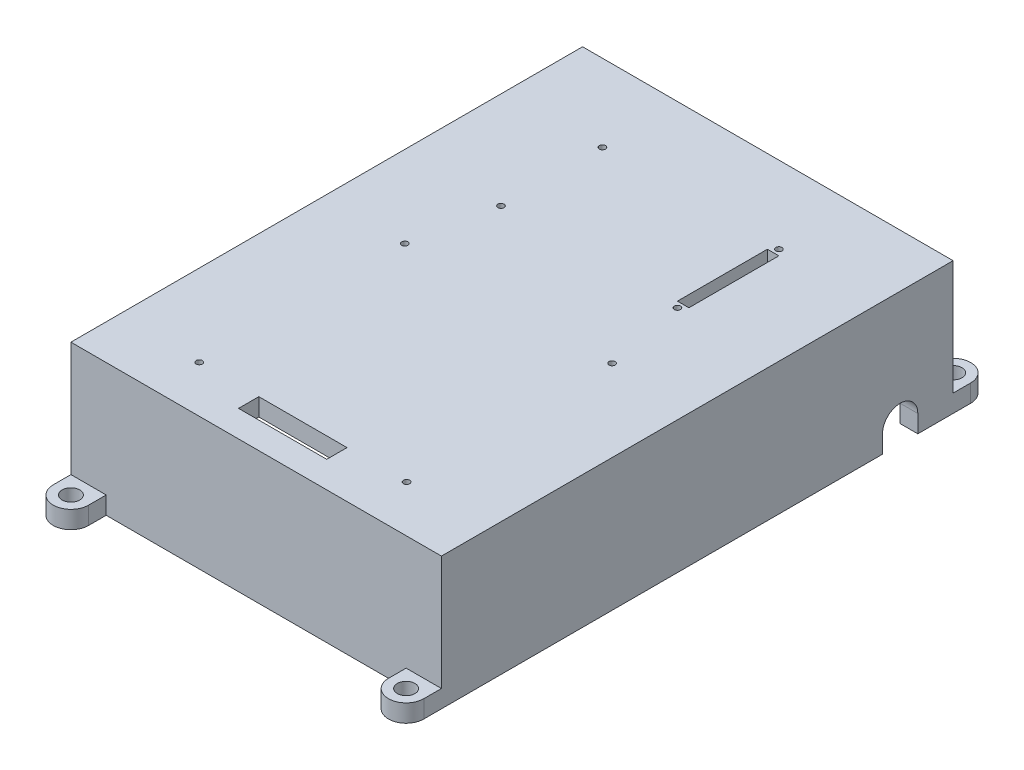
SolidWorks part; units mm, degrees
ref_plane "Front Plane" through (0, 0, 0) normal (0, 0, 1) x (1, 0, 0)
ref_plane "Top Plane" through (0, 0, 0) normal (0, 1, 0) x (1, 0, 0)
ref_plane "Right Plane" through (0, 0, 0) normal (1, 0, 0) x (0, 0, -1)
sketch "Sketch1" plane through (0, 0, 0) normal (0, 1, 0) x (1, 0, 0)
  line L1 (-53.34, -73.66) -> (53.34, -73.66)
  line L2 (-53.34, -73.66) -> (-53.34, 73.66)
  line L3 (-53.34, 73.66) -> (53.34, 73.66)
  line L4 (53.34, -73.66) -> (53.34, 73.66)
  line L5 (-53.34, -73.66) -> (53.34, 73.66) construction
  line L6 (-53.34, 73.66) -> (53.34, -73.66) construction
  point P0 (0, 0)
  dimension "D1" = 147.32
  dimension "D2" = 106.68
extrude "Boss-Extrude1" add sketch "Sketch1" along normal blind 38.1
shell "Shell1" thickness 5.08
sketch "Sketch5" plane through (0, 38.1, 0) normal (0, 1, 0) x (1, 0, 0)
  line L5 (0, 73.66) -> (0, 0)
  line L7 (-29.845, -60.198) -> (29.845, -60.198) construction
  line L8 (-29.845, -60.198) -> (-29.845, -1.016) construction
  line L9 (-29.845, -1.016) -> (29.845, -1.016) construction
  line L10 (29.845, -60.198) -> (29.845, -1.016) construction
  line L11 (-29.845, -60.198) -> (29.845, -1.016) construction
  line L12 (-29.845, -1.016) -> (29.845, -60.198) construction
  line L13 (-25.4, 22.225) -> (25.4, 22.225) construction
  line L14 (-12.7, -60.198) -> (12.7, -66.04) construction
  line L19 (-25.4, 22.225) -> (-25.4, 51.435) construction
  line L20 (-25.4, 51.435) -> (25.4, 51.435) construction
  line L21 (-12.7, -60.198) -> (12.7, -60.198)
  line L22 (-12.7, -60.198) -> (-12.7, -66.04)
  line L23 (-12.7, -66.04) -> (12.7, -66.04)
  line L24 (12.7, -60.198) -> (12.7, -66.04)
  line L25 (12.7, -60.198) -> (-12.7, -66.04) construction
  line L26 (-53.34, -73.66) -> (53.34, -73.66) construction
  line L27 (25.4, 22.225) -> (25.4, 51.435) construction
  line L28 (-25.4, 22.225) -> (25.4, 51.435) construction
  line L29 (-25.4, 51.435) -> (25.4, 22.225) construction
  line L30 (53.34, 73.66) -> (-53.34, 73.66) construction
  line L32 (23.749, 23.876) -> (27.051, 23.876)
  line L33 (23.749, 23.876) -> (23.749, 49.784)
  line L34 (23.749, 49.784) -> (27.051, 49.784)
  line L35 (27.051, 23.876) -> (27.051, 49.784)
  line L36 (23.749, 23.876) -> (27.051, 49.784) construction
  line L37 (23.749, 49.784) -> (27.051, 23.876) construction
  circle A0 centre (-29.845, -1.016) radius 0.889
  circle A1 centre (29.845, -1.016) radius 0.889
  circle A2 centre (29.845, -60.198) radius 0.889
  circle A3 centre (-29.845, -60.198) radius 0.889
  circle A8 centre (-25.4, 51.435) radius 0.889
  circle A9 centre (25.4, 51.435) radius 0.889
  circle A10 centre (25.4, 22.225) radius 0.889
  circle A11 centre (-25.4, 22.225) radius 0.889
  point P0 (0, 36.83)
  point P5 (0, -30.607)
  point P19 (0, 36.83)
  point P23 (25.4, 36.83)
  point P31 (0, -63.119)
  dimension "D5" = 1.778
  dimension "D6" = 29.21
  dimension "D8" = 1.778
  dimension "D2" = 50.8
  dimension "D3" = 59.182
  dimension "D4" = 59.69
  dimension "D7" = 7.62
  dimension "D9" = 25.908
  dimension "D10" = 3.302
  dimension "D12" = 5.842
  dimension "D13" = 25.4
extrude "Cut-Extrude1" cut sketch "Sketch5" against normal blind 38.1 contours A8 | A11 | L32 L35 L34 L33 | A9 | A10 | L24 L21 L22 L23 | A2 | A3 | A0 | A1
sketch "Sketch6" plane through (-53.34, 0, 0) normal (-1, 0, 0) x (0, 0, 1)
  line L0 (-58.42, -17.4211) -> (-58.42, 5.08) construction
  line L1 (-63.5, -17.4211) -> (-63.5, 5.08)
  line L2 (-53.34, -17.4211) -> (-53.34, 5.08)
  line L3 (-73.66, 38.1) -> (-73.66, 0) construction
  line L4 (-73.66, 0) -> (73.66, 0) construction
  arc A0 (-63.5, -17.4211) -> (-53.34, -17.4211) centre (-58.42, -17.4211) ccw
  arc A1 (-53.34, 5.08) -> (-63.5, 5.08) centre (-58.42, 5.08) ccw
  point P2 (-58.42, -6.1706)
  dimension "D2" = 5.08
  dimension "D1" = 15.24
  dimension "D3" = 5.08
extrude "Cut-Extrude2" cut sketch "Sketch6" against normal through all
sketch "Sketch15" plane through (0, 0, 0) normal (0, -1, 0) x (1, 0, 0)
  line L0 (-48.26, -78.74) -> (-48.26, 78.74) construction
  line L1 (-53.34, -78.74) -> (-53.34, 78.74)
  line L2 (-43.18, -78.74) -> (-43.18, 78.74)
  line L5 (-53.34, 73.66) -> (53.34, 73.66) construction
  line L8 (0, 0) -> (0, 22.7776) construction
  line L9 (48.26, -78.74) -> (48.26, 78.74) construction
  line L10 (53.34, -78.74) -> (53.34, 78.74)
  line L11 (43.18, -78.74) -> (43.18, 78.74)
  line L13 (48.26, -53.34) -> (53.34, -53.34)
  line L14 (48.26, -53.34) -> (53.34, -53.34)
  line L15 (-48.26, -63.5) -> (-53.34, -63.5)
  line L16 (-48.26, -63.5) -> (-53.34, -63.5)
  line L21 (-53.34, -63.5) -> (-53.34, -73.66)
  line L22 (-53.34, -73.66) -> (53.34, -73.66)
  line L23 (53.34, -73.66) -> (53.34, -63.5)
  line L24 (-53.34, -53.34) -> (-48.26, -53.34)
  line L25 (53.34, -53.34) -> (53.34, 73.66)
  line L26 (53.34, 73.66) -> (-53.34, 73.66)
  line L27 (-53.34, 73.66) -> (-53.34, -53.34)
  line L28 (-53.34, -53.34) -> (-48.26, -53.34)
  line L29 (-48.26, -53.34) -> (-48.26, 68.58)
  line L30 (-48.26, -53.34) -> (-48.26, 68.58)
  line L31 (-48.26, 68.58) -> (48.26, 68.58)
  line L32 (-48.26, 68.58) -> (48.26, 68.58)
  line L33 (48.26, 68.58) -> (48.26, -53.34)
  line L34 (48.26, 68.58) -> (48.26, -53.34)
  line L35 (53.34, -63.5) -> (48.26, -63.5)
  line L37 (53.34, -53.34) -> (53.34, 73.66)
  line L38 (53.34, 73.66) -> (-53.34, 73.66)
  line L39 (-53.34, 73.66) -> (-53.34, -53.34)
  line L48 (53.34, -63.5) -> (48.26, -63.5)
  line L49 (48.26, -63.5) -> (48.26, -68.58)
  line L50 (48.26, -63.5) -> (48.26, -68.58)
  line L51 (48.26, -68.58) -> (-48.26, -68.58)
  line L53 (-53.34, -63.5) -> (-53.34, -73.66)
  line L54 (-53.34, -73.66) -> (53.34, -73.66)
  line L55 (53.34, -73.66) -> (53.34, -63.5)
  line L60 (48.26, -68.58) -> (-48.26, -68.58)
  line L61 (-48.26, -68.58) -> (-48.26, -63.5)
  line L62 (-48.26, -68.58) -> (-48.26, -63.5)
  arc A0 (-53.34, -78.74) -> (-43.18, -78.74) centre (-48.26, -78.74) ccw
  arc A1 (-43.18, 78.74) -> (-53.34, 78.74) centre (-48.26, 78.74) ccw
  circle A2 centre (-48.26, 78.74) radius 2.54
  circle A3 centre (-48.26, -78.74) radius 2.54
  arc A4 (53.34, -78.74) -> (43.18, -78.74) centre (48.26, -78.74) cw
  arc A5 (43.18, 78.74) -> (53.34, 78.74) centre (48.26, 78.74) cw
  circle A6 centre (48.26, -78.74) radius 2.54
  circle A7 centre (48.26, 78.74) radius 2.54
  point P2 (-48.26, 0)
  point P17 (48.26, 0)
  line M28 (53.34, 73.66) -> (-53.34, 73.66)
  dimension "D1" = 5.08
  dimension "D3" = 5.08
  dimension "D4" = 5.08
  dimension "D2" = 5.08
  dimension "D5" = 0
  dimension "D6" = 0
extrude "Boss-Extrude5" add sketch "Sketch15" against normal blind 5.08 contours L1 A0 L2 L54 A3 | A4 L10 L54 L11 A6 | A5 L11 L10 A7 M28 | L2 A1 L1 A2 M28
